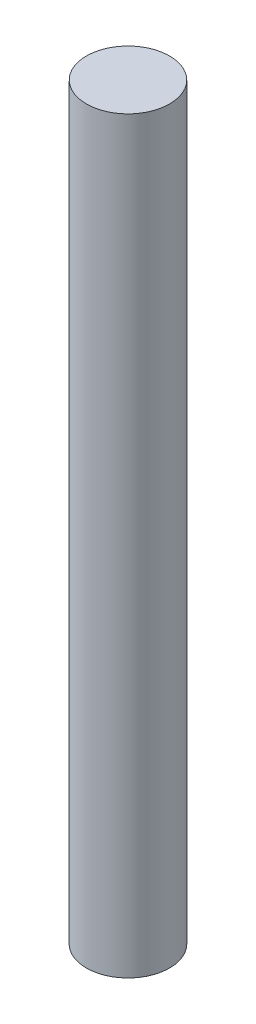
SolidWorks part; units mm, degrees
ref_plane "Front Plane" through (0, 0, 0) normal (0, 0, 1) x (1, 0, 0)
ref_plane "Top Plane" through (0, 0, 0) normal (0, 1, 0) x (1, 0, 0)
ref_plane "Right Plane" through (0, 0, 0) normal (1, 0, 0) x (0, 0, -1)
sketch "Sketch1" plane through (0, 0, 0) normal (0, 1, 0) x (1, 0, 0)
  circle A0 centre (0, 0) radius 1.5875
  dimension "D1" = 3.175
extrude "Boss-Extrude1" add sketch "Sketch1" along normal blind 28.575
